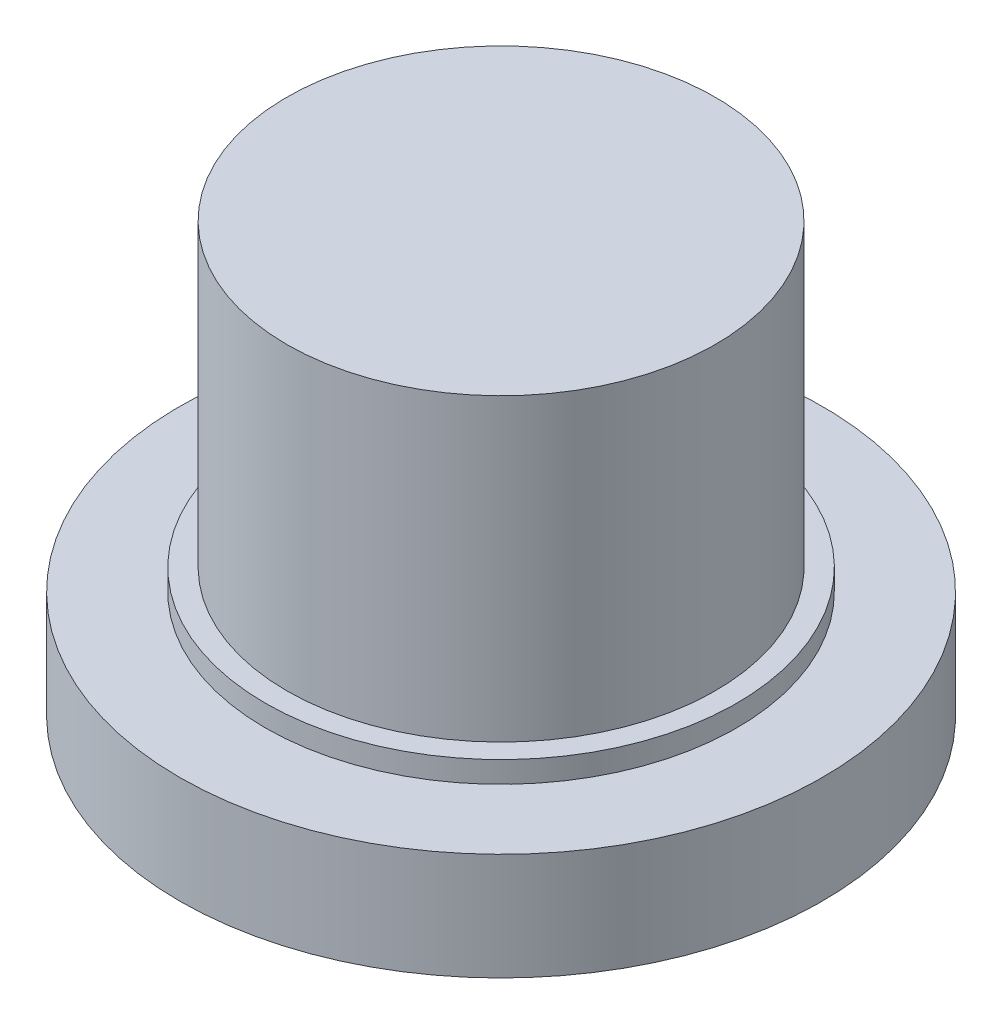
SolidWorks part; units mm, degrees
ref_plane "Front Plane" through (0, 0, 0) normal (0, 0, 1) x (1, 0, 0)
ref_plane "Top Plane" through (0, 0, 0) normal (0, 1, 0) x (1, 0, 0)
ref_plane "Right Plane" through (0, 0, 0) normal (1, 0, 0) x (0, 0, -1)
sketch "Sketch1" plane through (0, 0, 0) normal (0, 1, 0) x (1, 0, 0)
  circle A0 centre (0, 0) radius 15
  dimension "D1" = 30
extrude "Boss-Extrude1" add sketch "Sketch1" along normal blind 5
sketch "Sketch2" plane through (0, 5, 0) normal (0, 1, 0) x (1, 0, 0)
  circle A0 centre (0, 0) radius 10
  dimension "D1" = 20
extrude "Boss-Extrude2" add sketch "Sketch2" along normal blind 15
sketch "Sketch3" plane through (0, 0, 0) normal (0, -1, 0) x (1, 0, 0)
  circle A0 centre (0, 0) radius 7.5
  dimension "D1" = 15
extrude "Cut-Extrude1" cut sketch "Sketch3" against normal blind 19
sketch "Sketch5" plane through (0, 5, 0) normal (0, 1, 0) x (1, 0, 0)
  circle A0 centre (0, 0) radius 11
  dimension "D1" = 22
extrude "Boss-Extrude3" add sketch "Sketch5" along normal blind 1
